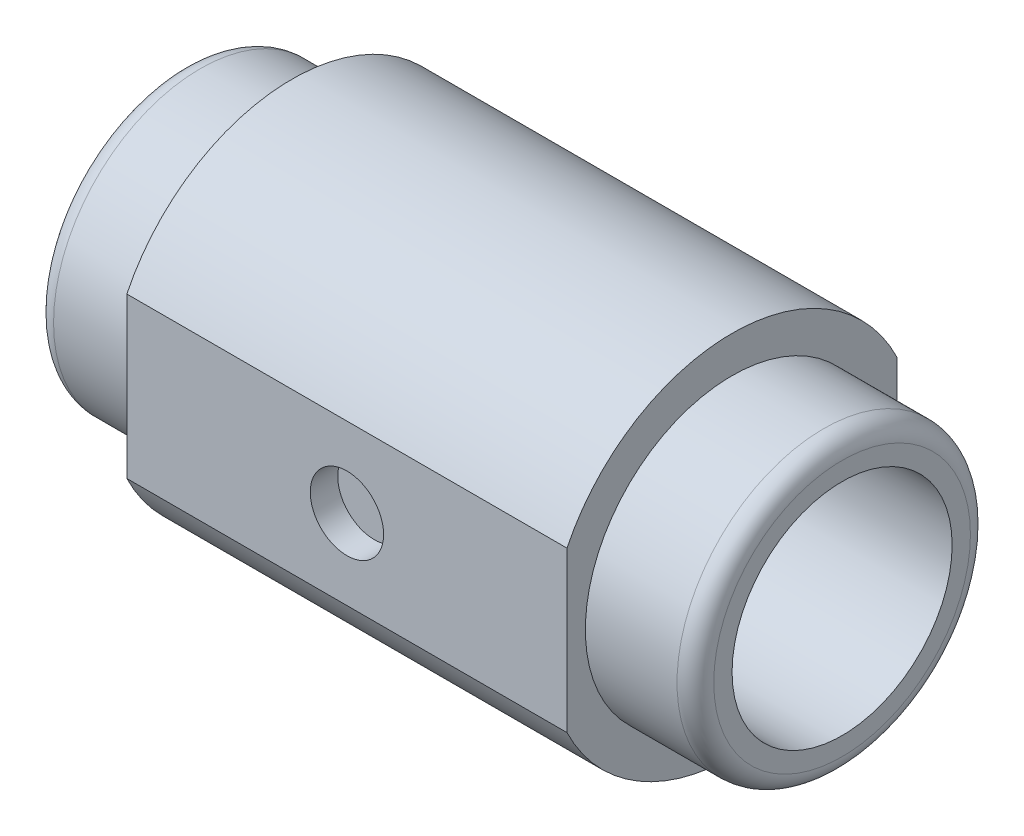
SolidWorks part; units mm, degrees
material "AISI 1035 Steel (SS)"
ref_plane "Front Plane" through (0, 0, 0) normal (0, 0, 1) x (1, 0, 0)
ref_plane "Top Plane" through (0, 0, 0) normal (0, 1, 0) x (1, 0, 0)
ref_plane "Right Plane" through (0, 0, 0) normal (1, 0, 0) x (0, 0, -1)
sketch "Sketch1" plane through (0, 0, 0) normal (1, 0, 0) x (0, 0, -1)
  line L1 (-7.2593, 3.5126) -> (-7.2593, -3.5126)
  line L2 (7.2593, 3.5126) -> (7.2593, -3.5126)
  arc A0 (-7.2593, -3.5126) -> (7.2593, -3.5126) centre (0, 0) ccw
  arc A1 (7.2593, 3.5126) -> (-7.2593, 3.5126) centre (0, 0) ccw
extrude "Boss-Extrude1" add sketch "Sketch1" along normal blind 9.6774 and the other way blind 9.6774
sketch "Sketch2" plane through (9.6774, 0, 0) normal (1, 0, 0) x (0, 0, -1)
  circle A0 centre (0, 0) radius 6.4516
extrude "Boss-Extrude2" add sketch "Sketch2" along normal blind 4.8387
mirror "Mirror1" about plane through (0, 0, 0) normal (1, 0, 0) of "Boss-Extrude2"
sketch "Sketch3" plane through (14.5161, 0, 0) normal (1, 0, 0) x (0, 0, -1)
  circle A0 centre (0, 0) radius 4.8387
extrude "Cut-Extrude1" cut sketch "Sketch3" against normal through all
fillet "Fillet1" radius 0.8077 2 edges at (-14.5161, 0, -6.4516) (14.5161, 0, -6.4516)
sketch "Sketch4" plane through (0, 0, 7.2593) normal (0, 0, 1) x (1, 0, 0)
  circle A0 centre (0, 0) radius 1.6129
extrude "Cut-Extrude2" cut sketch "Sketch4" against normal blind 1.209
